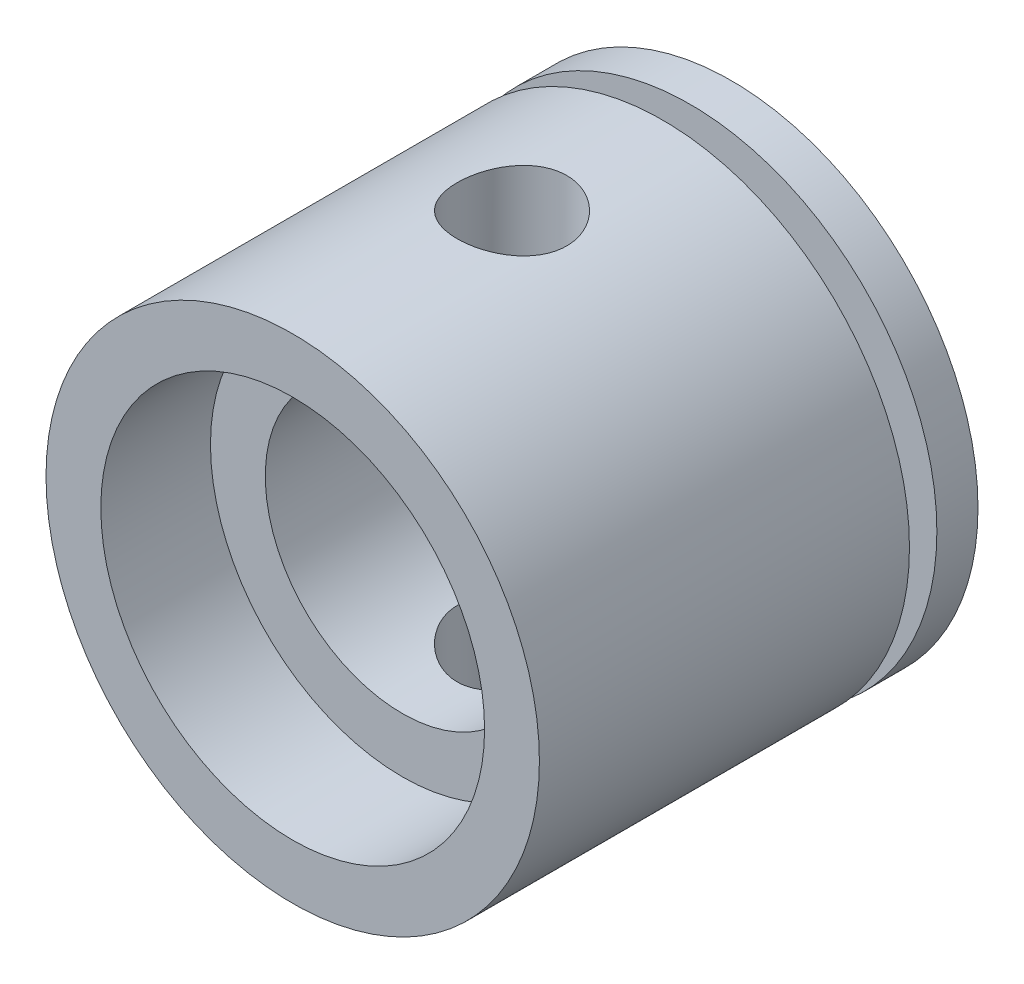
SolidWorks part; units mm, degrees
ref_plane "Front Plane" through (0, 0, 0) normal (0, 0, 1) x (1, 0, 0)
ref_plane "Top Plane" through (0, 0, 0) normal (0, 1, 0) x (1, 0, 0)
ref_plane "Right Plane" through (0, 0, 0) normal (1, 0, 0) x (0, 0, -1)
sketch "Sketch1" plane through (0, 0, 0) normal (0, 0, 1) x (1, 0, 0)
  circle A0 centre (0, 0) radius 9
  dimension "D1" = 18
extrude "Boss-Extrude1" add sketch "Sketch1" along normal blind 16
hole_wizard "CBORE for M14 Hex Head Bolt1" positions "Sketch3" profile "Sketch2" counterbore size "M14" standard "ANSI Metric"
sketch "Sketch3" plane through (0, 0, 16) normal (0, 0, 1) x (1, 0, 0)
  point P0 (0, 0)
sketch "Sketch2" plane through (0, 0, 16) normal (1, 0, 0) x (0, -1, 0)
  line L0 (0, 0) -> (0, 14)
  line L1 (0, 14) -> (5, 14)
  line L2 (5, 14) -> (5, 4)
  line L3 (5, 4) -> (7, 4)
  line L4 (7, 4) -> (7, 0)
  line L5 (7, 0) -> (0, 0)
  line L10 (0, 14) -> (-5, 14) construction
  line L11 (0, -6.35) -> (0, 107.95) construction
  dimension "Hole Dia." = 10
  dimension "Hole Depth" = 14
  dimension "C'Bore Dia." = 14
  dimension "C'Bore Depth" = 4
  dimension "Drill Angle" = 180
ref_plane "Plane1" through (0, 0, 2.5) normal (0, 0, 1) x (1, 0, 0)
sketch "Sketch4" plane through (0, 0, 2.5) normal (0, 0, 1) x (1, 0, 0)
  circle A0 centre (0, 0) radius 9 construction
  circle A1 centre (0, 0) radius 9
  circle A2 centre (0, 0) radius 7.5
  dimension "D1" = 15
extrude "Cut-Extrude1" cut sketch "Sketch4" against normal blind 1
sketch "Sketch5" plane through (0, 0, 0) normal (0, 1, 0) x (1, 0, 0)
  line L0 (9, 0) -> (-9, 0) construction
  circle A0 centre (0, -8) radius 2
  dimension "D2" = 4
  dimension "D1" = 8
extrude "Cut-Extrude2" cut sketch "Sketch5" against normal mid plane 31
